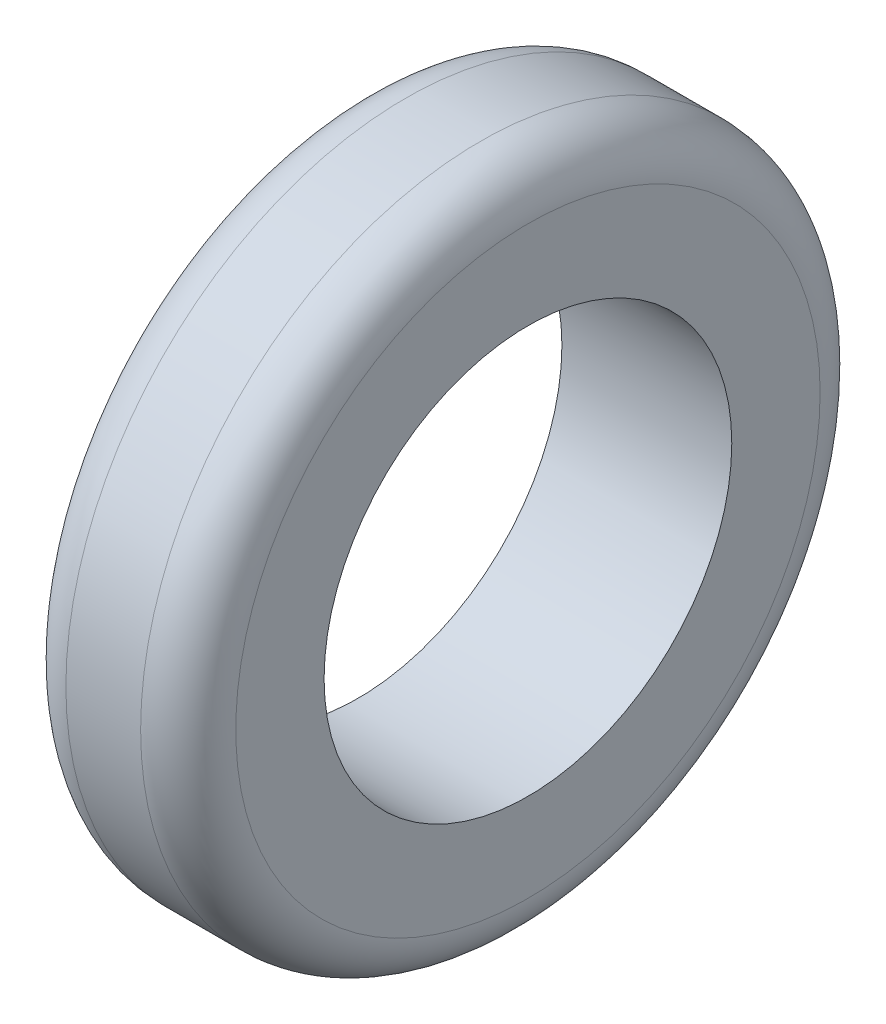
SolidWorks part; units mm, degrees
material "SBR"
ref_plane "Front Plane" through (0, 0, 0) normal (0, 0, 1) x (1, 0, 0)
ref_plane "Top Plane" through (0, 0, 0) normal (0, 1, 0) x (1, 0, 0)
ref_plane "Right Plane" through (0, 0, 0) normal (1, 0, 0) x (0, 0, -1)
sketch "Sketch1" plane through (0, 0, 0) normal (1, 0, 0) x (0, 0, -1)
  circle A0 centre (0, 0) radius 30
  circle A1 centre (0, 0) radius 50
  dimension "D1" = 60
  dimension "D2" = 100
extrude "Boss-Extrude1" add sketch "Sketch1" along normal blind 25
fillet "Fillet1" radius 7 2 edges at (0, 0, -50) (25, 0, -50)
